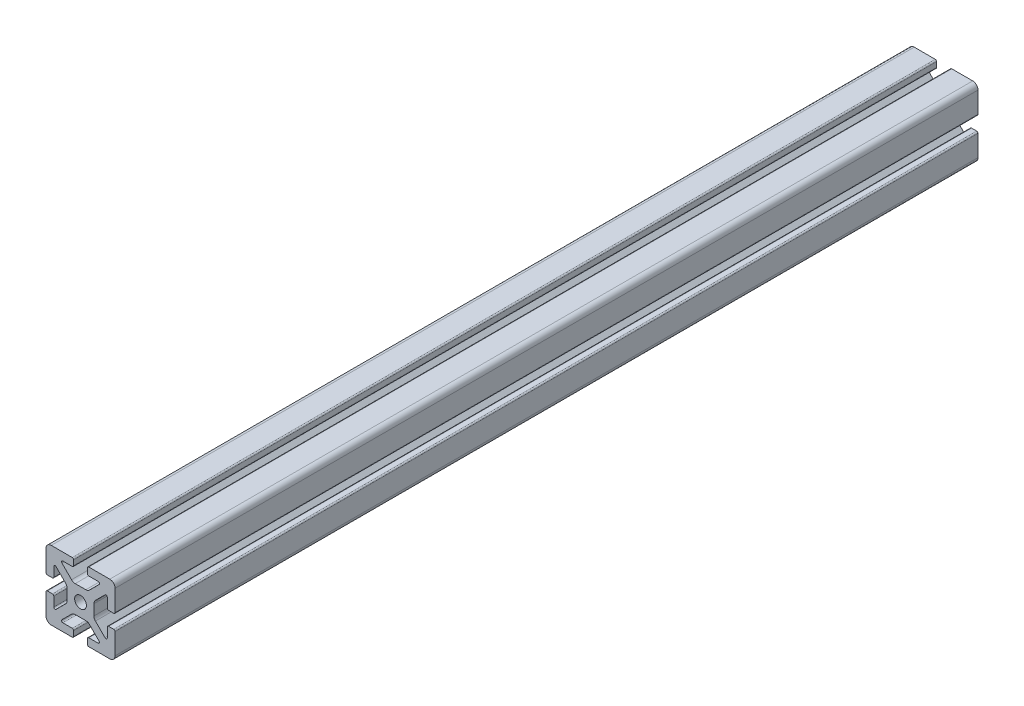
SolidWorks part; units mm, degrees
ref_plane "Front Plane" through (0, 0, 0) normal (0, 0, 1) x (1, 0, 0)
ref_plane "Top Plane" through (0, 0, 0) normal (0, 1, 0) x (1, 0, 0)
ref_plane "Right Plane" through (0, 0, 0) normal (1, 0, 0) x (0, 0, -1)
sketch "Sketch1" plane through (0, 0, 0) normal (0, 0, 1) x (1, 0, 0)
  line L2 (-20, 16.952) -> (-20, 4.7625)
  line L3 (-16.952, 20) -> (-4.7625, 20)
  line L4 (-4.0005, 19.238) -> (-4.0005, 16.2662)
  line L5 (-4.7625, 15.5042) -> (-10.2235, 15.5042)
  line L6 (-10.7623, 14.2034) -> (-5.194, 8.6351)
  line L7 (-14.2034, 10.7623) -> (-8.6351, 5.194)
  line L8 (-15.5042, 10.2235) -> (-15.5042, 4.7625)
  line L9 (-16.2662, 4.0005) -> (-19.238, 4.0005)
  line L11 (-3.0746, 7.7572) -> (3.0746, 7.7572)
  line L12 (-7.7572, 3.0746) -> (-7.7572, -3.0746)
  line L13 (16.2662, 4.0005) -> (19.238, 4.0005)
  line L14 (15.5042, 10.2235) -> (15.5042, 4.7625)
  line L15 (20, 16.952) -> (20, 4.7625)
  line L16 (16.952, 20) -> (4.7625, 20)
  line L17 (4.0005, 19.238) -> (4.0005, 16.2662)
  line L18 (4.7625, 15.5042) -> (10.2235, 15.5042)
  line L19 (7.7572, 3.0746) -> (7.7572, -3.0746)
  line L20 (10.7623, 14.2034) -> (5.194, 8.6351)
  line L21 (14.2034, 10.7623) -> (8.6351, 5.194)
  line L22 (-16.2662, -4.0005) -> (-19.238, -4.0005)
  line L23 (-15.5042, -10.2235) -> (-15.5042, -4.7625)
  line L24 (-14.2034, -10.7623) -> (-8.6351, -5.194)
  line L25 (-10.7623, -14.2034) -> (-5.194, -8.6351)
  line L26 (-4.7625, -15.5042) -> (-10.2235, -15.5042)
  line L27 (-4.0005, -19.238) -> (-4.0005, -16.2662)
  line L28 (-16.952, -20) -> (-4.7625, -20)
  line L29 (-20, -16.952) -> (-20, -4.7625)
  line L30 (20, -16.952) -> (20, -4.7625)
  line L31 (16.952, -20) -> (4.7625, -20)
  line L32 (4.0005, -19.238) -> (4.0005, -16.2662)
  line L33 (4.7625, -15.5042) -> (10.2235, -15.5042)
  line L34 (10.7623, -14.2034) -> (5.194, -8.6351)
  line L35 (14.2034, -10.7623) -> (8.6351, -5.194)
  line L36 (15.5042, -10.2235) -> (15.5042, -4.7625)
  line L37 (16.2662, -4.0005) -> (19.238, -4.0005)
  line L38 (-3.0746, -7.7572) -> (3.0746, -7.7572)
  circle A0 centre (0, 0) radius 3.4036
  arc A1 (-20, 16.952) -> (-16.952, 20) centre (-16.952, 16.952) cw
  arc A2 (-14.2034, 10.7623) -> (-15.5042, 10.2235) centre (-14.7422, 10.2235) ccw
  arc A3 (-10.2235, 15.5042) -> (-10.7623, 14.2034) centre (-10.2235, 14.7422) ccw
  arc A4 (-4.7625, 20) -> (-4.0005, 19.238) centre (-4.7625, 19.238) cw
  arc A5 (-20, 4.7625) -> (-19.238, 4.0005) centre (-19.238, 4.7625) ccw
  arc A6 (-15.5042, 4.7625) -> (-16.2662, 4.0005) centre (-16.2662, 4.7625) cw
  arc A7 (-4.0005, 16.2662) -> (-4.7625, 15.5042) centre (-4.7625, 16.2662) cw
  arc A8 (-3.0746, 7.7572) -> (-5.194, 8.6351) centre (-3.0746, 10.7544) cw
  arc A9 (-7.7572, 3.0746) -> (-8.6351, 5.194) centre (-10.7544, 3.0746) ccw
  arc A10 (15.5042, 4.7625) -> (16.2662, 4.0005) centre (16.2662, 4.7625) ccw
  arc A11 (20, 4.7625) -> (19.238, 4.0005) centre (19.238, 4.7625) cw
  arc A12 (20, 16.952) -> (16.952, 20) centre (16.952, 16.952) ccw
  arc A13 (4.7625, 20) -> (4.0005, 19.238) centre (4.7625, 19.238) ccw
  arc A14 (4.0005, 16.2662) -> (4.7625, 15.5042) centre (4.7625, 16.2662) ccw
  arc A15 (3.0746, 7.7572) -> (5.194, 8.6351) centre (3.0746, 10.7544) ccw
  arc A16 (7.7572, 3.0746) -> (8.6351, 5.194) centre (10.7544, 3.0746) cw
  arc A17 (14.2034, 10.7623) -> (15.5042, 10.2235) centre (14.7422, 10.2235) cw
  arc A18 (10.2235, 15.5042) -> (10.7623, 14.2034) centre (10.2235, 14.7422) cw
  arc A19 (-7.7572, -3.0746) -> (-8.6351, -5.194) centre (-10.7544, -3.0746) cw
  arc A20 (-3.0746, -7.7572) -> (-5.194, -8.6351) centre (-3.0746, -10.7544) ccw
  arc A21 (-4.0005, -16.2662) -> (-4.7625, -15.5042) centre (-4.7625, -16.2662) ccw
  arc A22 (-15.5042, -4.7625) -> (-16.2662, -4.0005) centre (-16.2662, -4.7625) ccw
  arc A23 (-20, -4.7625) -> (-19.238, -4.0005) centre (-19.238, -4.7625) cw
  arc A24 (-4.7625, -20) -> (-4.0005, -19.238) centre (-4.7625, -19.238) ccw
  arc A25 (-10.2235, -15.5042) -> (-10.7623, -14.2034) centre (-10.2235, -14.7422) cw
  arc A26 (-14.2034, -10.7623) -> (-15.5042, -10.2235) centre (-14.7422, -10.2235) cw
  arc A27 (-20, -16.952) -> (-16.952, -20) centre (-16.952, -16.952) ccw
  arc A28 (20, -16.952) -> (16.952, -20) centre (16.952, -16.952) cw
  arc A29 (14.2034, -10.7623) -> (15.5042, -10.2235) centre (14.7422, -10.2235) ccw
  arc A30 (10.2235, -15.5042) -> (10.7623, -14.2034) centre (10.2235, -14.7422) ccw
  arc A31 (4.7625, -20) -> (4.0005, -19.238) centre (4.7625, -19.238) cw
  arc A32 (20, -4.7625) -> (19.238, -4.0005) centre (19.238, -4.7625) ccw
  arc A33 (15.5042, -4.7625) -> (16.2662, -4.0005) centre (16.2662, -4.7625) cw
  arc A34 (4.0005, -16.2662) -> (4.7625, -15.5042) centre (4.7625, -16.2662) cw
  arc A35 (3.0746, -7.7572) -> (5.194, -8.6351) centre (3.0746, -10.7544) cw
  arc A36 (7.7572, -3.0746) -> (8.6351, -5.194) centre (10.7544, -3.0746) ccw
extrude "Boss-Extrude1" add sketch "Sketch1" along normal mid plane 500
